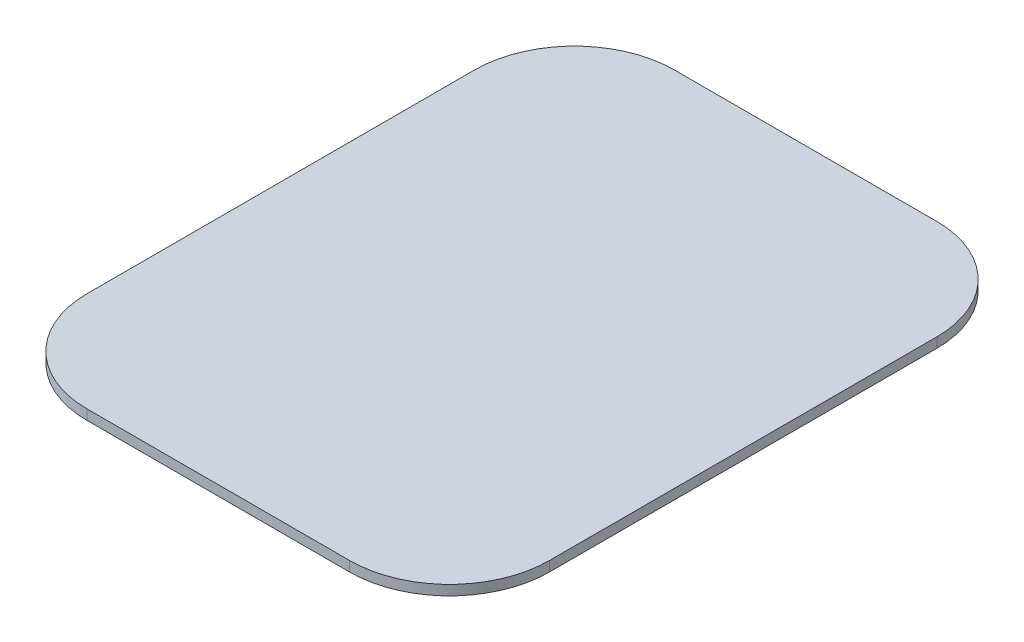
SolidWorks part; units mm, degrees
ref_plane "Front Plane" through (0, 0, 0) normal (0, 0, 1) x (1, 0, 0)
ref_plane "Top Plane" through (0, 0, 0) normal (0, 1, 0) x (1, 0, 0)
ref_plane "Right Plane" through (0, 0, 0) normal (1, 0, 0) x (0, 0, -1)
sketch "Sketch1" plane through (0, 0, 0) normal (0, 1, 0) x (1, 0, 0)
  line L1 (-92.5, -117.5) -> (92.5, -117.5)
  line L2 (-92.5, -117.5) -> (-92.5, 117.5)
  line L3 (-92.5, 117.5) -> (92.5, 117.5)
  line L4 (92.5, -117.5) -> (92.5, 117.5)
  line L5 (-92.5, -117.5) -> (92.5, 117.5) construction
  line L6 (-92.5, 117.5) -> (92.5, -117.5) construction
  point P0 (0, 0)
  dimension "D1" = 185
  dimension "D2" = 235
extrude "Boss-Extrude1" add sketch "Sketch1" along normal blind 4
fillet "Fillet1" radius 40 4 edges at (-92.5, 2, -117.5) (92.5, 2, -117.5) (92.5, 2, 117.5) (-92.5, 2, 117.5)
